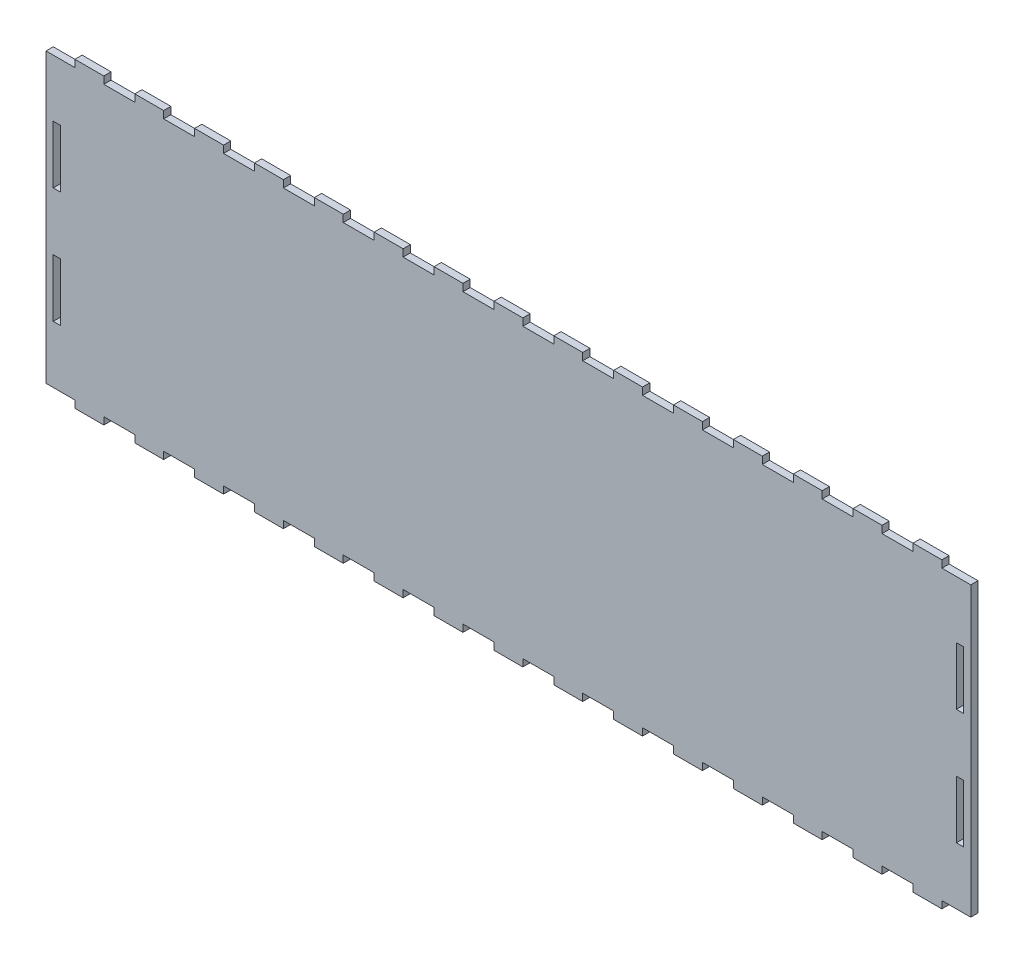
SolidWorks part; units mm, degrees
ref_plane "Front Plane" through (0, 0, 0) normal (0, 0, 1) x (1, 0, 0)
ref_plane "Top Plane" through (0, 0, 0) normal (0, 1, 0) x (1, 0, 0)
ref_plane "Right Plane" through (0, 0, 0) normal (1, 0, 0) x (0, 0, -1)
sketch "Sketch1" plane through (0, 0, 0) normal (0, 0, 1) x (1, 0, 0)
  line L8 (400.05, 101.3524) -> (400.05, 75.9523)
  line L9 (403.225, 101.3524) -> (400.05, 101.3524)
  line L10 (403.225, 75.9523) -> (403.225, 101.3524)
  line L11 (400.05, 75.9523) -> (403.225, 75.9523)
  line L16 (400.05, 50.5523) -> (400.05, 25.1523)
  line L17 (403.225, 50.5523) -> (400.05, 50.5523)
  line L18 (403.225, 25.1523) -> (403.225, 50.5523)
  line L19 (400.05, 25.1523) -> (403.225, 25.1523)
  line L24 (6.35, 75.9524) -> (6.35, 101.3524)
  line L25 (3.175, 75.9524) -> (6.35, 75.9524)
  line L26 (3.175, 101.3524) -> (3.175, 75.9524)
  line L27 (6.35, 101.3524) -> (3.175, 101.3524)
  line L32 (6.35, 25.1523) -> (6.35, 50.5523)
  line L33 (3.175, 25.1523) -> (6.35, 25.1523)
  line L34 (3.175, 50.5523) -> (3.175, 25.1523)
  line L35 (6.35, 50.5523) -> (3.175, 50.5523)
  line L400 (65.3143, 126.5047) -> (65.2143, 126.5047)
  line L401 (65.2143, 126.5047) -> (51.8071, 126.5047)
  line L402 (51.8071, 126.5047) -> (51.7071, 126.5047)
  line L403 (51.7071, 126.5047) -> (51.7071, 129.6797)
  line L404 (51.7071, 129.6797) -> (39.0071, 129.6797)
  line L405 (39.0071, 129.6797) -> (39.0071, 126.5047)
  line L406 (39.0071, 126.5047) -> (38.9071, 126.5047)
  line L407 (38.9071, 126.5047) -> (25.5, 126.5047)
  line L408 (25.5, 126.5047) -> (25.4, 126.5047)
  line L409 (25.4, 126.5047) -> (25.4, 129.6797)
  line L410 (25.4, 129.6797) -> (12.7, 129.6797)
  line L411 (12.7, 129.6797) -> (12.7, 126.5047)
  line L412 (12.7, 126.5047) -> (12.6, 126.5047)
  line L413 (12.6, 126.5047) -> (0, 126.5047)
  line L414 (0, 126.5047) -> (0, 0)
  line L415 (0, 0) -> (12.6, 0)
  line L416 (12.6, 0) -> (12.7, 0)
  line L417 (12.7, 0) -> (12.7, -3.175)
  line L418 (12.7, -3.175) -> (25.4, -3.175)
  line L419 (25.4, -3.175) -> (25.4, 0)
  line L420 (25.4, 0) -> (25.5, 0)
  line L421 (25.5, 0) -> (38.9071, 0)
  line L422 (38.9071, 0) -> (39.0071, 0)
  line L423 (39.0071, 0) -> (39.0071, -3.175)
  line L424 (39.0071, -3.175) -> (51.7071, -3.175)
  line L425 (51.7071, -3.175) -> (51.7071, 0)
  line L426 (51.7071, 0) -> (51.8071, 0)
  line L427 (51.8071, 0) -> (65.2143, 0)
  line L428 (65.2143, 0) -> (65.3143, 0)
  line L429 (65.3143, 0) -> (65.3143, -3.175)
  line L430 (65.3143, -3.175) -> (78.0143, -3.175)
  line L431 (78.0143, -3.175) -> (78.0143, 0)
  line L432 (78.0143, 0) -> (78.1143, 0)
  line L433 (78.1143, 0) -> (91.5214, 0)
  line L434 (91.5214, 0) -> (91.6214, 0)
  line L435 (91.6214, 0) -> (91.6214, -3.175)
  line L436 (91.6214, -3.175) -> (104.3214, -3.175)
  line L437 (104.3214, -3.175) -> (104.3214, 0)
  line L438 (104.3214, 0) -> (104.4214, 0)
  line L439 (104.4214, 0) -> (117.8286, 0)
  line L440 (117.8286, 0) -> (117.9286, 0)
  line L441 (117.9286, 0) -> (117.9286, -3.175)
  line L442 (117.9286, -3.175) -> (130.6286, -3.175)
  line L443 (130.6286, -3.175) -> (130.6286, 0)
  line L444 (130.6286, 0) -> (130.7286, 0)
  line L445 (130.7286, 0) -> (144.1357, 0)
  line L446 (144.1357, 0) -> (144.2357, 0)
  line L447 (144.2357, 0) -> (144.2357, -3.175)
  line L448 (144.2357, -3.175) -> (156.9357, -3.175)
  line L449 (156.9357, -3.175) -> (156.9357, 0)
  line L450 (156.9357, 0) -> (157.0357, 0)
  line L451 (157.0357, 0) -> (170.4429, 0)
  line L452 (170.4429, 0) -> (170.5429, 0)
  line L453 (170.5429, 0) -> (170.5429, -3.175)
  line L454 (170.5429, -3.175) -> (183.2429, -3.175)
  line L455 (183.2429, -3.175) -> (183.2429, 0)
  line L456 (183.2429, 0) -> (183.3429, 0)
  line L457 (183.3429, 0) -> (196.75, 0)
  line L458 (196.75, 0) -> (196.85, 0)
  line L459 (196.85, 0) -> (196.85, -3.175)
  line L460 (196.85, -3.175) -> (209.55, -3.175)
  line L461 (209.55, -3.175) -> (209.55, 0)
  line L462 (209.55, 0) -> (209.65, 0)
  line L463 (209.65, 0) -> (223.0571, 0)
  line L464 (223.0571, 0) -> (223.1571, 0)
  line L465 (223.1571, 0) -> (223.1571, -3.175)
  line L466 (223.1571, -3.175) -> (235.8571, -3.175)
  line L467 (235.8571, -3.175) -> (235.8571, 0)
  line L468 (235.8571, 0) -> (235.9571, 0)
  line L469 (235.9571, 0) -> (249.3643, 0)
  line L470 (249.3643, 0) -> (249.4643, 0)
  line L471 (249.4643, 0) -> (249.4643, -3.175)
  line L472 (249.4643, -3.175) -> (262.1643, -3.175)
  line L473 (262.1643, -3.175) -> (262.1643, 0)
  line L474 (262.1643, 0) -> (262.2643, 0)
  line L475 (262.2643, 0) -> (275.6714, 0)
  line L476 (275.6714, 0) -> (275.7714, 0)
  line L477 (275.7714, 0) -> (275.7714, -3.175)
  line L478 (275.7714, -3.175) -> (288.4714, -3.175)
  line L479 (288.4714, -3.175) -> (288.4714, 0)
  line L480 (288.4714, 0) -> (288.5714, 0)
  line L481 (288.5714, 0) -> (301.9786, 0)
  line L482 (301.9786, 0) -> (302.0786, 0)
  line L483 (302.0786, 0) -> (302.0786, -3.175)
  line L484 (302.0786, -3.175) -> (314.7786, -3.175)
  line L485 (314.7786, -3.175) -> (314.7786, 0)
  line L486 (314.7786, 0) -> (314.8786, 0)
  line L487 (314.8786, 0) -> (328.2857, 0)
  line L488 (328.2857, 0) -> (328.3857, 0)
  line L489 (328.3857, 0) -> (328.3857, -3.175)
  line L490 (328.3857, -3.175) -> (341.0857, -3.175)
  line L491 (341.0857, -3.175) -> (341.0857, 0)
  line L492 (341.0857, 0) -> (341.1857, 0)
  line L493 (341.1857, 0) -> (354.5929, 0)
  line L494 (354.5929, 0) -> (354.6929, 0)
  line L495 (354.6929, 0) -> (354.6929, -3.175)
  line L496 (354.6929, -3.175) -> (367.3929, -3.175)
  line L497 (367.3929, -3.175) -> (367.3929, 0)
  line L498 (367.3929, 0) -> (367.4929, 0)
  line L499 (367.4929, 0) -> (380.9, 0)
  line L500 (380.9, 0) -> (381, 0)
  line L501 (381, 0) -> (381, -3.175)
  line L502 (381, -3.175) -> (393.7, -3.175)
  line L503 (393.7, -3.175) -> (393.7, 0)
  line L504 (393.7, 0) -> (393.8, 0)
  line L505 (393.8, 0) -> (406.4, 0)
  line L506 (406.4, 0) -> (406.4, 126.5047)
  line L507 (406.4, 126.5047) -> (393.8, 126.5047)
  line L508 (393.8, 126.5047) -> (393.7, 126.5047)
  line L509 (393.7, 126.5047) -> (393.7, 129.6797)
  line L510 (393.7, 129.6797) -> (381, 129.6797)
  line L511 (381, 129.6797) -> (381, 126.5047)
  line L512 (381, 126.5047) -> (380.9, 126.5047)
  line L513 (380.9, 126.5047) -> (367.4929, 126.5047)
  line L514 (367.4929, 126.5047) -> (367.3929, 126.5047)
  line L515 (367.3929, 126.5047) -> (367.3929, 129.6797)
  line L516 (367.3929, 129.6797) -> (354.6929, 129.6797)
  line L517 (354.6929, 129.6797) -> (354.6929, 126.5047)
  line L518 (354.6929, 126.5047) -> (354.5929, 126.5047)
  line L519 (354.5929, 126.5047) -> (341.1857, 126.5047)
  line L520 (341.1857, 126.5047) -> (341.0857, 126.5047)
  line L521 (341.0857, 126.5047) -> (341.0857, 129.6797)
  line L522 (341.0857, 129.6797) -> (328.3857, 129.6797)
  line L523 (328.3857, 129.6797) -> (328.3857, 126.5047)
  line L524 (328.3857, 126.5047) -> (328.2857, 126.5047)
  line L525 (328.2857, 126.5047) -> (314.8786, 126.5047)
  line L526 (314.8786, 126.5047) -> (314.7786, 126.5047)
  line L527 (314.7786, 126.5047) -> (314.7786, 129.6797)
  line L528 (314.7786, 129.6797) -> (302.0786, 129.6797)
  line L529 (302.0786, 129.6797) -> (302.0786, 126.5047)
  line L530 (302.0786, 126.5047) -> (301.9786, 126.5047)
  line L531 (301.9786, 126.5047) -> (288.5714, 126.5047)
  line L532 (288.5714, 126.5047) -> (288.4714, 126.5047)
  line L533 (288.4714, 126.5047) -> (288.4714, 129.6797)
  line L534 (288.4714, 129.6797) -> (275.7714, 129.6797)
  line L535 (275.7714, 129.6797) -> (275.7714, 126.5047)
  line L536 (275.7714, 126.5047) -> (275.6714, 126.5047)
  line L537 (275.6714, 126.5047) -> (262.2643, 126.5047)
  line L538 (262.2643, 126.5047) -> (262.1643, 126.5047)
  line L539 (262.1643, 126.5047) -> (262.1643, 129.6797)
  line L540 (262.1643, 129.6797) -> (249.4643, 129.6797)
  line L541 (249.4643, 129.6797) -> (249.4643, 126.5047)
  line L542 (249.4643, 126.5047) -> (249.3643, 126.5047)
  line L543 (249.3643, 126.5047) -> (235.9571, 126.5047)
  line L544 (235.9571, 126.5047) -> (235.8571, 126.5047)
  line L545 (235.8571, 126.5047) -> (235.8571, 129.6797)
  line L546 (235.8571, 129.6797) -> (223.1571, 129.6797)
  line L547 (223.1571, 129.6797) -> (223.1571, 126.5047)
  line L548 (223.1571, 126.5047) -> (223.0571, 126.5047)
  line L549 (223.0571, 126.5047) -> (209.65, 126.5047)
  line L550 (209.65, 126.5047) -> (209.55, 126.5047)
  line L551 (209.55, 126.5047) -> (209.55, 129.6797)
  line L552 (209.55, 129.6797) -> (196.85, 129.6797)
  line L553 (196.85, 129.6797) -> (196.85, 126.5047)
  line L554 (196.85, 126.5047) -> (196.75, 126.5047)
  line L555 (196.75, 126.5047) -> (183.3429, 126.5047)
  line L556 (183.3429, 126.5047) -> (183.2429, 126.5047)
  line L557 (183.2429, 126.5047) -> (183.2429, 129.6797)
  line L558 (183.2429, 129.6797) -> (170.5429, 129.6797)
  line L559 (170.5429, 129.6797) -> (170.5429, 126.5047)
  line L560 (170.5429, 126.5047) -> (170.4429, 126.5047)
  line L561 (170.4429, 126.5047) -> (157.0357, 126.5047)
  line L562 (157.0357, 126.5047) -> (156.9357, 126.5047)
  line L563 (156.9357, 126.5047) -> (156.9357, 129.6797)
  line L564 (156.9357, 129.6797) -> (144.2357, 129.6797)
  line L565 (144.2357, 129.6797) -> (144.2357, 126.5047)
  line L566 (144.2357, 126.5047) -> (144.1357, 126.5047)
  line L567 (144.1357, 126.5047) -> (130.7286, 126.5047)
  line L568 (130.7286, 126.5047) -> (130.6286, 126.5047)
  line L569 (130.6286, 126.5047) -> (130.6286, 129.6797)
  line L570 (130.6286, 129.6797) -> (117.9286, 129.6797)
  line L571 (117.9286, 129.6797) -> (117.9286, 126.5047)
  line L572 (117.9286, 126.5047) -> (117.8286, 126.5047)
  line L573 (117.8286, 126.5047) -> (104.4214, 126.5047)
  line L574 (104.4214, 126.5047) -> (104.3214, 126.5047)
  line L575 (104.3214, 126.5047) -> (104.3214, 129.6797)
  line L576 (104.3214, 129.6797) -> (91.6214, 129.6797)
  line L577 (91.6214, 129.6797) -> (91.6214, 126.5047)
  line L578 (91.6214, 126.5047) -> (91.5214, 126.5047)
  line L579 (91.5214, 126.5047) -> (78.1143, 126.5047)
  line L580 (78.1143, 126.5047) -> (78.0143, 126.5047)
  line L581 (78.0143, 126.5047) -> (78.0143, 129.6797)
  line L582 (78.0143, 129.6797) -> (65.3143, 129.6797)
  line L583 (65.3143, 129.6797) -> (65.3143, 126.5047)
extrude "Boss-Extrude1" add sketch "Sketch1" along normal blind 3.175 contours L414 L415 L416 L417 L418 L419 L420 L421 L422 L423 L424 L425 L426 L427 L428 L429 L430 L431 L432 L433 L434 L435 L436 L437 L438 L439 L440 L441 L442 L443 L444 L445 L446 L447 L448 L449 L450 L451 L452 L453 L454 L455 L456 L457 L458 L459 L460 L461 L462 L463 L464 L465 L466 L467 L468 L469 L470 L471 L472 L473 L474 L475 L476 L477 L478 L479 L480 L481 L482 L483 L484 L485 L486 L487 L488 L489 L490 L491 L492 L493 L494 L495 L496 L497 L498 L499 L500 L501 L502 L503 L504 L505 L506 L507 L508 L509 L510 L511 L512 L513 L514 L515 L516 L517 L518 L519 L520 L521 L522 L523 L524 L525 L526 L527 L528 L529 L530 L531 L532 L533 L534 L535 L536 L537 L538 L539 L540 L541 L542 L543 L544 L545 L546 L547 L548 L549 L550 L551 L552 L553 L554 L555 L556 L557 L558 L559 L560 L561 L562 L563 L564 L565 L566 L567 L568 L569 L570 L571 L572 L573 L574 L575 L576 L577 L578 L579 L580 L581 L582 L583 L400 L401 L402 L403 L404 L405 L406 L407 L408 L409 L410 L411 L412 L413
sketch "DXF" plane through (0, 0, 0) normal (0, 0, 1) x (1, 0, 0)
  line L0 (400.1516, 101.2508) -> (400.1516, 76.054)
  line L1 (400.1516, 76.054) -> (403.1234, 76.054)
  line L2 (403.1234, 76.054) -> (403.1234, 101.2508)
  line L3 (403.1234, 101.2508) -> (400.1516, 101.2508)
  line L4 (400.1516, 50.4507) -> (400.1516, 25.2539)
  line L5 (400.1516, 25.2539) -> (403.1234, 25.2539)
  line L6 (403.1234, 25.2539) -> (403.1234, 50.4507)
  line L7 (403.1234, 50.4507) -> (400.1516, 50.4507)
  line L8 (400.05, 101.3524) -> (400.05, 75.9523) construction
  line L9 (403.225, 101.3524) -> (400.05, 101.3524) construction
  line L10 (403.225, 75.9523) -> (403.225, 101.3524) construction
  line L11 (400.05, 75.9523) -> (403.225, 75.9523) construction
  line L12 (6.2484, 76.054) -> (6.2484, 101.2508)
  line L13 (6.2484, 101.2508) -> (3.2766, 101.2508)
  line L14 (3.2766, 101.2508) -> (3.2766, 76.054)
  line L15 (3.2766, 76.054) -> (6.2484, 76.054)
  line L16 (400.05, 50.5523) -> (400.05, 25.1523) construction
  line L17 (403.225, 50.5523) -> (400.05, 50.5523) construction
  line L18 (403.225, 25.1523) -> (403.225, 50.5523) construction
  line L19 (400.05, 25.1523) -> (403.225, 25.1523) construction
  line L20 (6.2484, 25.2539) -> (6.2484, 50.4507)
  line L21 (6.2484, 50.4507) -> (3.2766, 50.4507)
  line L22 (3.2766, 50.4507) -> (3.2766, 25.2539)
  line L23 (3.2766, 25.2539) -> (6.2484, 25.2539)
  line L24 (6.35, 75.9524) -> (6.35, 101.3524) construction
  line L25 (3.175, 75.9524) -> (6.35, 75.9524) construction
  line L26 (3.175, 101.3524) -> (3.175, 75.9524) construction
  line L27 (6.35, 101.3524) -> (3.175, 101.3524) construction
  line L28 (38.9055, 126.6063) -> (25.5016, 126.6063)
  line L29 (25.5016, 126.6063) -> (25.5016, 126.6063)
  line L30 (25.5016, 126.6063) -> (25.5016, 129.7813)
  line L31 (25.5016, 129.7813) -> (12.5984, 129.7813)
  line L32 (6.35, 25.1523) -> (6.35, 50.5523) construction
  line L33 (3.175, 25.1523) -> (6.35, 25.1523) construction
  line L34 (3.175, 50.5523) -> (3.175, 25.1523) construction
  line L35 (6.35, 50.5523) -> (3.175, 50.5523) construction
  line L36 (12.5984, 129.7813) -> (12.5984, 126.6063)
  line L37 (12.5984, 126.6063) -> (12.5984, 126.6063)
  line L38 (12.5984, 126.6063) -> (-0.1016, 126.6063)
  line L39 (-0.1016, 126.6063) -> (-0.1016, -0.1016)
  line L40 (-0.1016, -0.1016) -> (12.5984, -0.1016)
  line L41 (12.5984, -0.1016) -> (12.5984, -0.1016)
  line L42 (12.5984, -0.1016) -> (12.5984, -3.2766)
  line L43 (12.5984, -3.2766) -> (25.5016, -3.2766)
  line L44 (25.5016, -3.2766) -> (25.5016, -0.1016)
  line L45 (25.5016, -0.1016) -> (25.5016, -0.1016)
  line L46 (25.5016, -0.1016) -> (38.9055, -0.1016)
  line L47 (38.9055, -0.1016) -> (38.9055, -0.1016)
  line L48 (38.9055, -0.1016) -> (38.9055, -3.2766)
  line L49 (38.9055, -3.2766) -> (51.8087, -3.2766)
  line L50 (51.8087, -3.2766) -> (51.8087, -0.1016)
  line L51 (51.8087, -0.1016) -> (51.8087, -0.1016)
  line L52 (51.8087, -0.1016) -> (65.2127, -0.1016)
  line L53 (65.2127, -0.1016) -> (65.2127, -0.1016)
  line L54 (65.2127, -0.1016) -> (65.2127, -3.2766)
  line L55 (65.2127, -3.2766) -> (78.1159, -3.2766)
  line L56 (78.1159, -3.2766) -> (78.1159, -0.1016)
  line L57 (78.1159, -0.1016) -> (78.1159, -0.1016)
  line L58 (78.1159, -0.1016) -> (91.5198, -0.1016)
  line L59 (91.5198, -0.1016) -> (91.5198, -0.1016)
  line L60 (91.5198, -0.1016) -> (91.5198, -3.2766)
  line L61 (91.5198, -3.2766) -> (104.423, -3.2766)
  line L62 (104.423, -3.2766) -> (104.423, -0.1016)
  line L63 (104.423, -0.1016) -> (104.423, -0.1016)
  line L64 (104.423, -0.1016) -> (117.827, -0.1016)
  line L65 (117.827, -0.1016) -> (117.827, -0.1016)
  line L66 (117.827, -0.1016) -> (117.827, -3.2766)
  line L67 (117.827, -3.2766) -> (130.7302, -3.2766)
  line L68 (130.7302, -3.2766) -> (130.7302, -0.1016)
  line L69 (130.7302, -0.1016) -> (130.7302, -0.1016)
  line L70 (130.7302, -0.1016) -> (144.1341, -0.1016)
  line L71 (144.1341, -0.1016) -> (144.1341, -0.1016)
  line L72 (144.1341, -0.1016) -> (144.1341, -3.2766)
  line L73 (144.1341, -3.2766) -> (157.0373, -3.2766)
  line L74 (157.0373, -3.2766) -> (157.0373, -0.1016)
  line L75 (157.0373, -0.1016) -> (157.0373, -0.1016)
  line L76 (157.0373, -0.1016) -> (170.4413, -0.1016)
  line L77 (170.4413, -0.1016) -> (170.4413, -0.1016)
  line L78 (170.4413, -0.1016) -> (170.4413, -3.2766)
  line L79 (170.4413, -3.2766) -> (183.3445, -3.2766)
  line L80 (183.3445, -3.2766) -> (183.3445, -0.1016)
  line L81 (183.3445, -0.1016) -> (183.3445, -0.1016)
  line L82 (183.3445, -0.1016) -> (196.7484, -0.1016)
  line L83 (196.7484, -0.1016) -> (196.7484, -0.1016)
  line L84 (196.7484, -0.1016) -> (196.7484, -3.2766)
  line L85 (196.7484, -3.2766) -> (209.6516, -3.2766)
  line L86 (209.6516, -3.2766) -> (209.6516, -0.1016)
  line L87 (209.6516, -0.1016) -> (209.6516, -0.1016)
  line L88 (209.6516, -0.1016) -> (223.0555, -0.1016)
  line L89 (223.0555, -0.1016) -> (223.0555, -0.1016)
  line L90 (223.0555, -0.1016) -> (223.0555, -3.2766)
  line L91 (223.0555, -3.2766) -> (235.9587, -3.2766)
  line L92 (235.9587, -3.2766) -> (235.9587, -0.1016)
  line L93 (235.9587, -0.1016) -> (235.9587, -0.1016)
  line L94 (235.9587, -0.1016) -> (249.3627, -0.1016)
  line L95 (249.3627, -0.1016) -> (249.3627, -0.1016)
  line L96 (249.3627, -0.1016) -> (249.3627, -3.2766)
  line L97 (249.3627, -3.2766) -> (262.2659, -3.2766)
  line L98 (262.2659, -3.2766) -> (262.2659, -0.1016)
  line L99 (262.2659, -0.1016) -> (262.2659, -0.1016)
  line L100 (262.2659, -0.1016) -> (275.6698, -0.1016)
  line L101 (275.6698, -0.1016) -> (275.6698, -0.1016)
  line L102 (275.6698, -0.1016) -> (275.6698, -3.2766)
  line L103 (275.6698, -3.2766) -> (288.573, -3.2766)
  line L104 (288.573, -3.2766) -> (288.573, -0.1016)
  line L105 (288.573, -0.1016) -> (288.573, -0.1016)
  line L106 (288.573, -0.1016) -> (301.977, -0.1016)
  line L107 (301.977, -0.1016) -> (301.977, -0.1016)
  line L108 (301.977, -0.1016) -> (301.977, -3.2766)
  line L109 (301.977, -3.2766) -> (314.8802, -3.2766)
  line L110 (314.8802, -3.2766) -> (314.8802, -0.1016)
  line L111 (314.8802, -0.1016) -> (314.8802, -0.1016)
  line L112 (314.8802, -0.1016) -> (328.2841, -0.1016)
  line L113 (328.2841, -0.1016) -> (328.2841, -0.1016)
  line L114 (328.2841, -0.1016) -> (328.2841, -3.2766)
  line L115 (328.2841, -3.2766) -> (341.1873, -3.2766)
  line L116 (341.1873, -3.2766) -> (341.1873, -0.1016)
  line L117 (341.1873, -0.1016) -> (341.1873, -0.1016)
  line L118 (341.1873, -0.1016) -> (354.5913, -0.1016)
  line L119 (354.5913, -0.1016) -> (354.5913, -0.1016)
  line L120 (354.5913, -0.1016) -> (354.5913, -3.2766)
  line L121 (354.5913, -3.2766) -> (367.4945, -3.2766)
  line L122 (367.4945, -3.2766) -> (367.4945, -0.1016)
  line L123 (367.4945, -0.1016) -> (367.4945, -0.1016)
  line L124 (367.4945, -0.1016) -> (380.8984, -0.1016)
  line L125 (380.8984, -0.1016) -> (380.8984, -0.1016)
  line L126 (380.8984, -0.1016) -> (380.8984, -3.2766)
  line L127 (380.8984, -3.2766) -> (393.8016, -3.2766)
  line L128 (393.8016, -3.2766) -> (393.8016, -0.1016)
  line L129 (393.8016, -0.1016) -> (393.8016, -0.1016)
  line L130 (393.8016, -0.1016) -> (406.5016, -0.1016)
  line L131 (406.5016, -0.1016) -> (406.5016, 126.6063)
  line L132 (406.5016, 126.6063) -> (393.8016, 126.6063)
  line L133 (393.8016, 126.6063) -> (393.8016, 126.6063)
  line L134 (393.8016, 126.6063) -> (393.8016, 129.7813)
  line L135 (393.8016, 129.7813) -> (380.8984, 129.7813)
  line L136 (380.8984, 129.7813) -> (380.8984, 126.6063)
  line L137 (380.8984, 126.6063) -> (380.8984, 126.6063)
  line L138 (380.8984, 126.6063) -> (367.4945, 126.6063)
  line L139 (367.4945, 126.6063) -> (367.4945, 126.6063)
  line L140 (367.4945, 126.6063) -> (367.4945, 129.7813)
  line L141 (367.4945, 129.7813) -> (354.5913, 129.7813)
  line L142 (354.5913, 129.7813) -> (354.5913, 126.6063)
  line L143 (354.5913, 126.6063) -> (354.5913, 126.6063)
  line L144 (354.5913, 126.6063) -> (341.1873, 126.6063)
  line L145 (341.1873, 126.6063) -> (341.1873, 126.6063)
  line L146 (341.1873, 126.6063) -> (341.1873, 129.7813)
  line L147 (341.1873, 129.7813) -> (328.2841, 129.7813)
  line L148 (328.2841, 129.7813) -> (328.2841, 126.6063)
  line L149 (328.2841, 126.6063) -> (328.2841, 126.6063)
  line L150 (328.2841, 126.6063) -> (314.8802, 126.6063)
  line L151 (314.8802, 126.6063) -> (314.8802, 126.6063)
  line L152 (314.8802, 126.6063) -> (314.8802, 129.7813)
  line L153 (314.8802, 129.7813) -> (301.977, 129.7813)
  line L154 (301.977, 129.7813) -> (301.977, 126.6063)
  line L155 (301.977, 126.6063) -> (301.977, 126.6063)
  line L156 (301.977, 126.6063) -> (288.573, 126.6063)
  line L157 (288.573, 126.6063) -> (288.573, 126.6063)
  line L158 (288.573, 126.6063) -> (288.573, 129.7813)
  line L159 (288.573, 129.7813) -> (275.6698, 129.7813)
  line L160 (275.6698, 129.7813) -> (275.6698, 126.6063)
  line L161 (275.6698, 126.6063) -> (275.6698, 126.6063)
  line L162 (275.6698, 126.6063) -> (262.2659, 126.6063)
  line L163 (262.2659, 126.6063) -> (262.2659, 126.6063)
  line L164 (262.2659, 126.6063) -> (262.2659, 129.7813)
  line L165 (262.2659, 129.7813) -> (249.3627, 129.7813)
  line L166 (249.3627, 129.7813) -> (249.3627, 126.6063)
  line L167 (249.3627, 126.6063) -> (249.3627, 126.6063)
  line L168 (249.3627, 126.6063) -> (235.9587, 126.6063)
  line L169 (235.9587, 126.6063) -> (235.9587, 126.6063)
  line L170 (235.9587, 126.6063) -> (235.9587, 129.7813)
  line L171 (235.9587, 129.7813) -> (223.0555, 129.7813)
  line L172 (223.0555, 129.7813) -> (223.0555, 126.6063)
  line L173 (223.0555, 126.6063) -> (223.0555, 126.6063)
  line L174 (223.0555, 126.6063) -> (209.6516, 126.6063)
  line L175 (209.6516, 126.6063) -> (209.6516, 126.6063)
  line L176 (209.6516, 126.6063) -> (209.6516, 129.7813)
  line L177 (209.6516, 129.7813) -> (196.7484, 129.7813)
  line L178 (196.7484, 129.7813) -> (196.7484, 126.6063)
  line L179 (196.7484, 126.6063) -> (196.7484, 126.6063)
  line L180 (196.7484, 126.6063) -> (183.3445, 126.6063)
  line L181 (183.3445, 126.6063) -> (183.3445, 126.6063)
  line L182 (183.3445, 126.6063) -> (183.3445, 129.7813)
  line L183 (183.3445, 129.7813) -> (170.4413, 129.7813)
  line L184 (170.4413, 129.7813) -> (170.4413, 126.6063)
  line L185 (170.4413, 126.6063) -> (170.4413, 126.6063)
  line L186 (170.4413, 126.6063) -> (157.0373, 126.6063)
  line L187 (157.0373, 126.6063) -> (157.0373, 126.6063)
  line L188 (157.0373, 126.6063) -> (157.0373, 129.7813)
  line L189 (157.0373, 129.7813) -> (144.1341, 129.7813)
  line L190 (144.1341, 129.7813) -> (144.1341, 126.6063)
  line L191 (144.1341, 126.6063) -> (144.1341, 126.6063)
  line L192 (144.1341, 126.6063) -> (130.7302, 126.6063)
  line L193 (130.7302, 126.6063) -> (130.7302, 126.6063)
  line L194 (130.7302, 126.6063) -> (130.7302, 129.7813)
  line L195 (130.7302, 129.7813) -> (117.827, 129.7813)
  line L196 (117.827, 129.7813) -> (117.827, 126.6063)
  line L197 (117.827, 126.6063) -> (117.827, 126.6063)
  line L198 (117.827, 126.6063) -> (104.423, 126.6063)
  line L199 (104.423, 126.6063) -> (104.423, 126.6063)
  line L200 (104.423, 126.6063) -> (104.423, 129.7813)
  line L201 (104.423, 129.7813) -> (91.5198, 129.7813)
  line L202 (91.5198, 129.7813) -> (91.5198, 126.6063)
  line L203 (91.5198, 126.6063) -> (91.5198, 126.6063)
  line L204 (91.5198, 126.6063) -> (78.1159, 126.6063)
  line L205 (78.1159, 126.6063) -> (78.1159, 126.6063)
  line L206 (78.1159, 126.6063) -> (78.1159, 129.7813)
  line L207 (78.1159, 129.7813) -> (65.2127, 129.7813)
  line L208 (65.2127, 129.7813) -> (65.2127, 126.6063)
  line L209 (65.2127, 126.6063) -> (65.2127, 126.6063)
  line L210 (65.2127, 126.6063) -> (51.8087, 126.6063)
  line L211 (51.8087, 126.6063) -> (51.8087, 126.6063)
  line L212 (51.8087, 126.6063) -> (51.8087, 129.7813)
  line L213 (51.8087, 129.7813) -> (38.9055, 129.7813)
  line L214 (38.9055, 129.7813) -> (38.9055, 126.6063)
  line L215 (38.9055, 126.6063) -> (38.9055, 126.6063)
  line L400 (65.3143, 126.5047) -> (65.2143, 126.5047) construction
  line L401 (65.2143, 126.5047) -> (51.8071, 126.5047) construction
  line L402 (51.8071, 126.5047) -> (51.7071, 126.5047) construction
  line L403 (51.7071, 126.5047) -> (51.7071, 129.6797) construction
  line L404 (51.7071, 129.6797) -> (39.0071, 129.6797) construction
  line L405 (39.0071, 129.6797) -> (39.0071, 126.5047) construction
  line L406 (39.0071, 126.5047) -> (38.9071, 126.5047) construction
  line L407 (38.9071, 126.5047) -> (25.5, 126.5047) construction
  line L408 (25.5, 126.5047) -> (25.4, 126.5047) construction
  line L409 (25.4, 126.5047) -> (25.4, 129.6797) construction
  line L410 (25.4, 129.6797) -> (12.7, 129.6797) construction
  line L411 (12.7, 129.6797) -> (12.7, 126.5047) construction
  line L412 (12.7, 126.5047) -> (12.6, 126.5047) construction
  line L413 (12.6, 126.5047) -> (0, 126.5047) construction
  line L414 (0, 126.5047) -> (0, 0) construction
  line L415 (0, 0) -> (12.6, 0) construction
  line L416 (12.6, 0) -> (12.7, 0) construction
  line L417 (12.7, 0) -> (12.7, -3.175) construction
  line L418 (12.7, -3.175) -> (25.4, -3.175) construction
  line L419 (25.4, -3.175) -> (25.4, 0) construction
  line L420 (25.4, 0) -> (25.5, 0) construction
  line L421 (25.5, 0) -> (38.9071, 0) construction
  line L422 (38.9071, 0) -> (39.0071, 0) construction
  line L423 (39.0071, 0) -> (39.0071, -3.175) construction
  line L424 (39.0071, -3.175) -> (51.7071, -3.175) construction
  line L425 (51.7071, -3.175) -> (51.7071, 0) construction
  line L426 (51.7071, 0) -> (51.8071, 0) construction
  line L427 (51.8071, 0) -> (65.2143, 0) construction
  line L428 (65.2143, 0) -> (65.3143, 0) construction
  line L429 (65.3143, 0) -> (65.3143, -3.175) construction
  line L430 (65.3143, -3.175) -> (78.0143, -3.175) construction
  line L431 (78.0143, -3.175) -> (78.0143, 0) construction
  line L432 (78.0143, 0) -> (78.1143, 0) construction
  line L433 (78.1143, 0) -> (91.5214, 0) construction
  line L434 (91.5214, 0) -> (91.6214, 0) construction
  line L435 (91.6214, 0) -> (91.6214, -3.175) construction
  line L436 (91.6214, -3.175) -> (104.3214, -3.175) construction
  line L437 (104.3214, -3.175) -> (104.3214, 0) construction
  line L438 (104.3214, 0) -> (104.4214, 0) construction
  line L439 (104.4214, 0) -> (117.8286, 0) construction
  line L440 (117.8286, 0) -> (117.9286, 0) construction
  line L441 (117.9286, 0) -> (117.9286, -3.175) construction
  line L442 (117.9286, -3.175) -> (130.6286, -3.175) construction
  line L443 (130.6286, -3.175) -> (130.6286, 0) construction
  line L444 (130.6286, 0) -> (130.7286, 0) construction
  line L445 (130.7286, 0) -> (144.1357, 0) construction
  line L446 (144.1357, 0) -> (144.2357, 0) construction
  line L447 (144.2357, 0) -> (144.2357, -3.175) construction
  line L448 (144.2357, -3.175) -> (156.9357, -3.175) construction
  line L449 (156.9357, -3.175) -> (156.9357, 0) construction
  line L450 (156.9357, 0) -> (157.0357, 0) construction
  line L451 (157.0357, 0) -> (170.4429, 0) construction
  line L452 (170.4429, 0) -> (170.5429, 0) construction
  line L453 (170.5429, 0) -> (170.5429, -3.175) construction
  line L454 (170.5429, -3.175) -> (183.2429, -3.175) construction
  line L455 (183.2429, -3.175) -> (183.2429, 0) construction
  line L456 (183.2429, 0) -> (183.3429, 0) construction
  line L457 (183.3429, 0) -> (196.75, 0) construction
  line L458 (196.75, 0) -> (196.85, 0) construction
  line L459 (196.85, 0) -> (196.85, -3.175) construction
  line L460 (196.85, -3.175) -> (209.55, -3.175) construction
  line L461 (209.55, -3.175) -> (209.55, 0) construction
  line L462 (209.55, 0) -> (209.65, 0) construction
  line L463 (209.65, 0) -> (223.0571, 0) construction
  line L464 (223.0571, 0) -> (223.1571, 0) construction
  line L465 (223.1571, 0) -> (223.1571, -3.175) construction
  line L466 (223.1571, -3.175) -> (235.8571, -3.175) construction
  line L467 (235.8571, -3.175) -> (235.8571, 0) construction
  line L468 (235.8571, 0) -> (235.9571, 0) construction
  line L469 (235.9571, 0) -> (249.3643, 0) construction
  line L470 (249.3643, 0) -> (249.4643, 0) construction
  line L471 (249.4643, 0) -> (249.4643, -3.175) construction
  line L472 (249.4643, -3.175) -> (262.1643, -3.175) construction
  line L473 (262.1643, -3.175) -> (262.1643, 0) construction
  line L474 (262.1643, 0) -> (262.2643, 0) construction
  line L475 (262.2643, 0) -> (275.6714, 0) construction
  line L476 (275.6714, 0) -> (275.7714, 0) construction
  line L477 (275.7714, 0) -> (275.7714, -3.175) construction
  line L478 (275.7714, -3.175) -> (288.4714, -3.175) construction
  line L479 (288.4714, -3.175) -> (288.4714, 0) construction
  line L480 (288.4714, 0) -> (288.5714, 0) construction
  line L481 (288.5714, 0) -> (301.9786, 0) construction
  line L482 (301.9786, 0) -> (302.0786, 0) construction
  line L483 (302.0786, 0) -> (302.0786, -3.175) construction
  line L484 (302.0786, -3.175) -> (314.7786, -3.175) construction
  line L485 (314.7786, -3.175) -> (314.7786, 0) construction
  line L486 (314.7786, 0) -> (314.8786, 0) construction
  line L487 (314.8786, 0) -> (328.2857, 0) construction
  line L488 (328.2857, 0) -> (328.3857, 0) construction
  line L489 (328.3857, 0) -> (328.3857, -3.175) construction
  line L490 (328.3857, -3.175) -> (341.0857, -3.175) construction
  line L491 (341.0857, -3.175) -> (341.0857, 0) construction
  line L492 (341.0857, 0) -> (341.1857, 0) construction
  line L493 (341.1857, 0) -> (354.5929, 0) construction
  line L494 (354.5929, 0) -> (354.6929, 0) construction
  line L495 (354.6929, 0) -> (354.6929, -3.175) construction
  line L496 (354.6929, -3.175) -> (367.3929, -3.175) construction
  line L497 (367.3929, -3.175) -> (367.3929, 0) construction
  line L498 (367.3929, 0) -> (367.4929, 0) construction
  line L499 (367.4929, 0) -> (380.9, 0) construction
  line L500 (380.9, 0) -> (381, 0) construction
  line L501 (381, 0) -> (381, -3.175) construction
  line L502 (381, -3.175) -> (393.7, -3.175) construction
  line L503 (393.7, -3.175) -> (393.7, 0) construction
  line L504 (393.7, 0) -> (393.8, 0) construction
  line L505 (393.8, 0) -> (406.4, 0) construction
  line L506 (406.4, 0) -> (406.4, 126.5047) construction
  line L507 (406.4, 126.5047) -> (393.8, 126.5047) construction
  line L508 (393.8, 126.5047) -> (393.7, 126.5047) construction
  line L509 (393.7, 126.5047) -> (393.7, 129.6797) construction
  line L510 (393.7, 129.6797) -> (381, 129.6797) construction
  line L511 (381, 129.6797) -> (381, 126.5047) construction
  line L512 (381, 126.5047) -> (380.9, 126.5047) construction
  line L513 (380.9, 126.5047) -> (367.4929, 126.5047) construction
  line L514 (367.4929, 126.5047) -> (367.3929, 126.5047) construction
  line L515 (367.3929, 126.5047) -> (367.3929, 129.6797) construction
  line L516 (367.3929, 129.6797) -> (354.6929, 129.6797) construction
  line L517 (354.6929, 129.6797) -> (354.6929, 126.5047) construction
  line L518 (354.6929, 126.5047) -> (354.5929, 126.5047) construction
  line L519 (354.5929, 126.5047) -> (341.1857, 126.5047) construction
  line L520 (341.1857, 126.5047) -> (341.0857, 126.5047) construction
  line L521 (341.0857, 126.5047) -> (341.0857, 129.6797) construction
  line L522 (341.0857, 129.6797) -> (328.3857, 129.6797) construction
  line L523 (328.3857, 129.6797) -> (328.3857, 126.5047) construction
  line L524 (328.3857, 126.5047) -> (328.2857, 126.5047) construction
  line L525 (328.2857, 126.5047) -> (314.8786, 126.5047) construction
  line L526 (314.8786, 126.5047) -> (314.7786, 126.5047) construction
  line L527 (314.7786, 126.5047) -> (314.7786, 129.6797) construction
  line L528 (314.7786, 129.6797) -> (302.0786, 129.6797) construction
  line L529 (302.0786, 129.6797) -> (302.0786, 126.5047) construction
  line L530 (302.0786, 126.5047) -> (301.9786, 126.5047) construction
  line L531 (301.9786, 126.5047) -> (288.5714, 126.5047) construction
  line L532 (288.5714, 126.5047) -> (288.4714, 126.5047) construction
  line L533 (288.4714, 126.5047) -> (288.4714, 129.6797) construction
  line L534 (288.4714, 129.6797) -> (275.7714, 129.6797) construction
  line L535 (275.7714, 129.6797) -> (275.7714, 126.5047) construction
  line L536 (275.7714, 126.5047) -> (275.6714, 126.5047) construction
  line L537 (275.6714, 126.5047) -> (262.2643, 126.5047) construction
  line L538 (262.2643, 126.5047) -> (262.1643, 126.5047) construction
  line L539 (262.1643, 126.5047) -> (262.1643, 129.6797) construction
  line L540 (262.1643, 129.6797) -> (249.4643, 129.6797) construction
  line L541 (249.4643, 129.6797) -> (249.4643, 126.5047) construction
  line L542 (249.4643, 126.5047) -> (249.3643, 126.5047) construction
  line L543 (249.3643, 126.5047) -> (235.9571, 126.5047) construction
  line L544 (235.9571, 126.5047) -> (235.8571, 126.5047) construction
  line L545 (235.8571, 126.5047) -> (235.8571, 129.6797) construction
  line L546 (235.8571, 129.6797) -> (223.1571, 129.6797) construction
  line L547 (223.1571, 129.6797) -> (223.1571, 126.5047) construction
  line L548 (223.1571, 126.5047) -> (223.0571, 126.5047) construction
  line L549 (223.0571, 126.5047) -> (209.65, 126.5047) construction
  line L550 (209.65, 126.5047) -> (209.55, 126.5047) construction
  line L551 (209.55, 126.5047) -> (209.55, 129.6797) construction
  line L552 (209.55, 129.6797) -> (196.85, 129.6797) construction
  line L553 (196.85, 129.6797) -> (196.85, 126.5047) construction
  line L554 (196.85, 126.5047) -> (196.75, 126.5047) construction
  line L555 (196.75, 126.5047) -> (183.3429, 126.5047) construction
  line L556 (183.3429, 126.5047) -> (183.2429, 126.5047) construction
  line L557 (183.2429, 126.5047) -> (183.2429, 129.6797) construction
  line L558 (183.2429, 129.6797) -> (170.5429, 129.6797) construction
  line L559 (170.5429, 129.6797) -> (170.5429, 126.5047) construction
  line L560 (170.5429, 126.5047) -> (170.4429, 126.5047) construction
  line L561 (170.4429, 126.5047) -> (157.0357, 126.5047) construction
  line L562 (157.0357, 126.5047) -> (156.9357, 126.5047) construction
  line L563 (156.9357, 126.5047) -> (156.9357, 129.6797) construction
  line L564 (156.9357, 129.6797) -> (144.2357, 129.6797) construction
  line L565 (144.2357, 129.6797) -> (144.2357, 126.5047) construction
  line L566 (144.2357, 126.5047) -> (144.1357, 126.5047) construction
  line L567 (144.1357, 126.5047) -> (130.7286, 126.5047) construction
  line L568 (130.7286, 126.5047) -> (130.6286, 126.5047) construction
  line L569 (130.6286, 126.5047) -> (130.6286, 129.6797) construction
  line L570 (130.6286, 129.6797) -> (117.9286, 129.6797) construction
  line L571 (117.9286, 129.6797) -> (117.9286, 126.5047) construction
  line L572 (117.9286, 126.5047) -> (117.8286, 126.5047) construction
  line L573 (117.8286, 126.5047) -> (104.4214, 126.5047) construction
  line L574 (104.4214, 126.5047) -> (104.3214, 126.5047) construction
  line L575 (104.3214, 126.5047) -> (104.3214, 129.6797) construction
  line L576 (104.3214, 129.6797) -> (91.6214, 129.6797) construction
  line L577 (91.6214, 129.6797) -> (91.6214, 126.5047) construction
  line L578 (91.6214, 126.5047) -> (91.5214, 126.5047) construction
  line L579 (91.5214, 126.5047) -> (78.1143, 126.5047) construction
  line L580 (78.1143, 126.5047) -> (78.0143, 126.5047) construction
  line L581 (78.0143, 126.5047) -> (78.0143, 129.6797) construction
  line L582 (78.0143, 129.6797) -> (65.3143, 129.6797) construction
  line L583 (65.3143, 129.6797) -> (65.3143, 126.5047) construction
  dimension "D1" = 0.1016
  dimension "D2" = 0.1016
extrude "DXF-Extrude" [suppressed] add sketch "DXF" along normal blind 3.175
